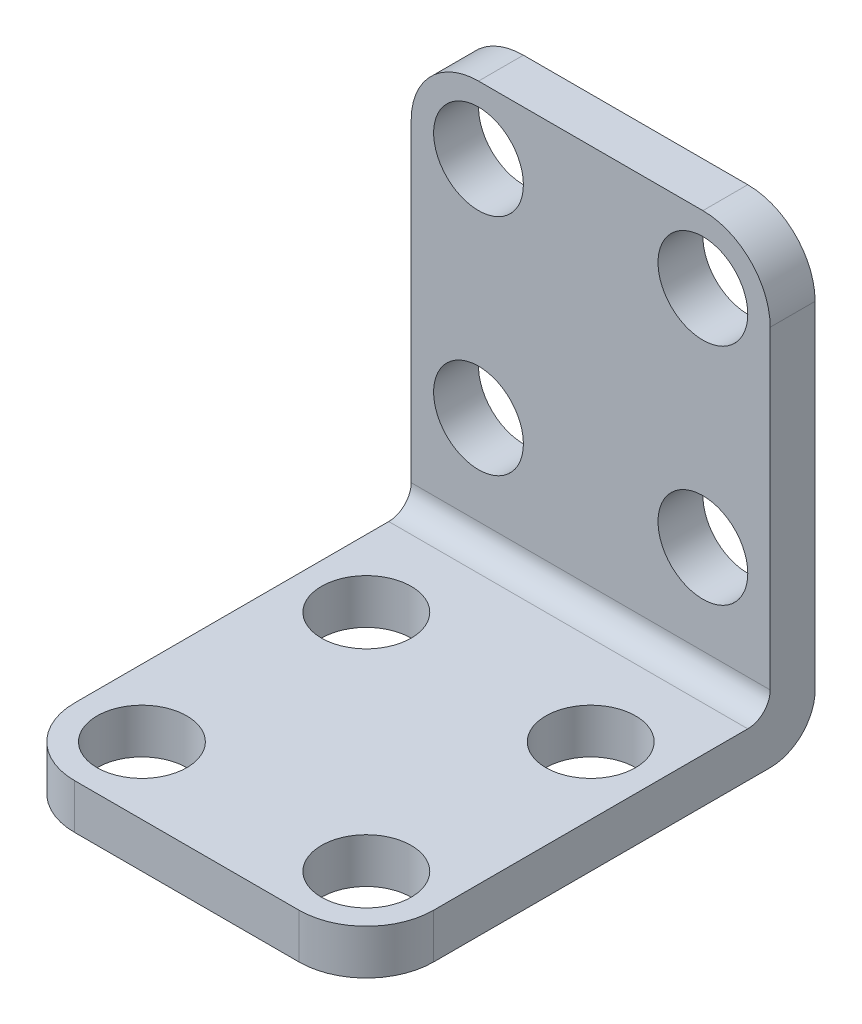
SolidWorks part; units mm, degrees
ref_plane "前视基准面" through (0, 0, 0) normal (0, 0, 1) x (1, 0, 0)
ref_plane "上视基准面" through (0, 0, 0) normal (0, 1, 0) x (1, 0, 0)
ref_plane "右视基准面" through (0, 0, 0) normal (1, 0, 0) x (0, 0, -1)
sketch "草图6" plane through (0, 0, 0) normal (0, 0, 1) x (1, 0, 0)
  line L1 (-20, -25) -> (20, -25)
  line L2 (-20, -25) -> (-20, 25)
  line L3 (-20, 25) -> (20, 25)
  line L4 (20, -25) -> (20, 25)
  line L5 (-20, -25) -> (20, 25) construction
  line L6 (-20, 25) -> (20, -25) construction
  point P0 (0, 0)
  dimension "D1" = 40
  dimension "D2" = 50
extrude "凸台-拉伸7" add sketch "草图6" along normal blind 5
sketch "草图12" plane through (0, 0, 5) normal (0, 0, 1) x (1, 0, 0)
  line L0 (20, -25) -> (20, 25) construction
  line L1 (-20, -25) -> (20, -25)
  line L2 (-20, -25) -> (-20, -20)
  line L3 (-20, -20) -> (20, -20)
  line L4 (20, -25) -> (20, -20)
  dimension "D1" = 5
extrude "凸台-拉伸8" add sketch "草图12" along normal blind 45
fillet "圆角9" radius 2.5 1 edges at (0, -20, 5)
fillet "圆角10" radius 5 1 edges at (0, -25, 0)
sketch "草图13" plane through (0, 0, 5) normal (0, 0, 1) x (1, 0, 0)
  line L0 (-20, 25) -> (-20, -17.5) construction
  line L1 (20, -17.5) -> (20, 25) construction
  line L2 (20, 25) -> (-20, 25) construction
  point P0 (-12.5, 17.5)
  point P1 (12.5, 17.5)
  point P2 (12.5, -7.5)
  point P3 (-12.5, -7.5)
  dimension "D1" = 25
  dimension "D2" = 25
  dimension "D3" = 25
  dimension "D4" = 25
  dimension "D5" = 35.3553
  dimension "D6" = 7.5
  dimension "D7" = 7.5
  dimension "D8" = 7.5
hole_wizard "大小mm 暗销孔2" positions "草图16" profile "草图17" hole size "Ø10.0" standard "GB" end condition through all
sketch "草图16" plane through (0, 0, 5) normal (0, 0, 1) x (1, 0, 0)
  point P0 (-12.5, 17.5)
  point P3 (-12.5, -7.5)
  point P6 (12.5, -7.5)
  point P9 (12.5, 17.5)
sketch "草图17" plane through (-12.5, 17.5, 5) normal (1, 0, 0) x (0, -1, 0)
  line L0 (0, 0) -> (0, 5)
  line L1 (0, 5) -> (5, 5)
  line L2 (5, 5) -> (5, 0)
  line L5 (5, 0) -> (0, 0)
  line L11 (0, -6.35) -> (0, 107.95) construction
  dimension "通孔孔直径" = 10
  dimension "通孔孔深度" = 5
fillet "圆角11" radius 7.5 4 edges at (-20, -22.5, 50) (20, -22.5, 50) (20, 25, 2.5) (-20, 25, 2.5)
sketch "草图18" plane through (0, -20, 0) normal (0, 1, 0) x (1, 0, 0)
  line L0 (12.5, -50) -> (-12.5, -50) construction
  line L1 (20, -42.5) -> (20, -7.5) construction
  point P0 (-12.5, -17.5)
  point P1 (-12.5, -42.5)
  point P2 (12.5, -42.5)
  point P3 (12.5, -17.5)
  dimension "D1" = 25
  dimension "D2" = 25
  dimension "D3" = 25
  dimension "D4" = 25
  dimension "D5" = 35.3553
  dimension "D6" = 35.3553
  dimension "D7" = 7.5
  dimension "D8" = 7.5
hole_wizard "大小mm 暗销孔3" positions "草图19" profile "草图20" hole size "Ø10.0" standard "GB" end condition through all
sketch "草图19" plane through (0, -20, 0) normal (0, 1, 0) x (1, 0, 0)
  point P0 (-12.5, -17.5)
  point P3 (12.5, -17.5)
  point P6 (12.5, -42.5)
  point P9 (-12.5, -42.5)
sketch "草图20" plane through (-12.5, -20, 17.5) normal (1, 0, 0) x (0, 0, 1)
  line L0 (0, 0) -> (0, 5)
  line L1 (0, 5) -> (5, 5)
  line L2 (5, 5) -> (5, 0)
  line L5 (5, 0) -> (0, 0)
  line L11 (0, -6.35) -> (0, 107.95) construction
  dimension "通孔孔直径" = 10
  dimension "通孔孔深度" = 5
